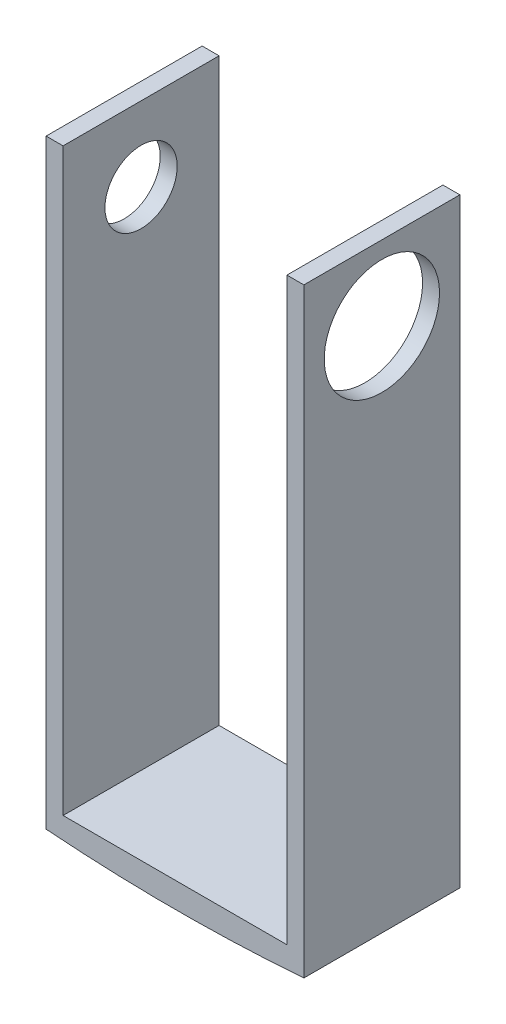
SolidWorks part; units mm, degrees
ref_plane "Front Plane" through (0, 0, 0) normal (0, 0, 1) x (1, 0, 0)
ref_plane "Top Plane" through (0, 0, 0) normal (0, 1, 0) x (1, 0, 0)
ref_plane "Right Plane" through (0, 0, 0) normal (1, 0, 0) x (0, 0, -1)
sketch "Sketch1" plane through (0, 0, 0) normal (0, 0, 1) x (1, 0, 0)
  line L0 (-3.3539, 20.1872) -> (-3.3539, -2.2918)
  line L1 (-3.3539, -2.2918) -> (6.2981, -2.2918)
  line L2 (6.2981, -2.2918) -> (6.2981, 20.1872)
  line L3 (5.6631, 20.1872) -> (5.6631, -1.5298)
  line L4 (5.6631, -1.5298) -> (-2.7189, -1.5298)
  line L5 (-2.7189, -1.5298) -> (-2.7189, 20.1872)
  line L6 (-2.7189, 20.1872) -> (-3.3539, 20.1872)
  line L7 (5.6631, 20.1872) -> (6.2981, 20.1872)
  dimension "D1" = 8.382
  dimension "D2" = 9.652
  dimension "D3" = 0.635
  dimension "D4" = 21.717
  dimension "D5" = 22.479
  dimension "D6" = 21.717
extrude "Boss-Extrude1" add sketch "Sketch1" along normal blind 5.842
sketch "Sketch2" plane through (-3.3539, 0, 0) normal (-1, 0, 0) x (0, 0, 1)
  line L0 (5.842, 20.1872) -> (0, 20.1872) construction
  line L1 (2.921, -2.2918) -> (2.921, 20.1872) construction
  point P0 (2.921, 17.3932)
  dimension "D1" = 2.794
hole_wizard "#6-32 Tapped Hole1" positions "Sketch3" profile "Sketch4" tap size "#6-32" standard "ANSI Inch" end condition up to next
sketch "Sketch3" plane through (-3.3539, 0, 0) normal (-1, 0, 0) x (0, 0, 1)
  point P0 (2.921, 17.3932)
sketch "Sketch4" plane through (-3.3539, 17.3932, 2.921) normal (0, 1, 0) x (0, 0, 1)
  line L0 (0, 0) -> (0, 0.635)
  line L1 (0, 0.635) -> (1.3525, 0.635)
  line L2 (1.3525, 0.635) -> (1.3525, 0)
  line L5 (1.3525, 0) -> (0, 0)
  line L11 (0, -6.35) -> (0, 107.95) construction
  dimension "Thread Major Dia." = 2.7051
  dimension "Thru Tap Drill Depth" = 0.635
sketch "Sketch5" plane through (6.2981, 0, 0) normal (1, 0, 0) x (0, 0, -1)
  point P0 (-2.921, 17.3932)
sketch "Sketch6" plane through (6.2981, 0, 0) normal (1, 0, 0) x (0, 0, -1)
  circle A0 centre (-2.921, 17.3932) radius 2.159
extrude "Cut-Extrude1" cut sketch "Sketch6" against normal up to next
sketch "Sketch12" plane through (-3.3539, 0, 0) normal (-1, 0, 0) x (0, 0, 1)
  line L0 (2.921, -2.2918) -> (2.921, 20.1872) construction
  line L1 (5.842, -2.2918) -> (0, -2.2918) construction
  line L2 (5.842, 20.1872) -> (0, 20.1872) construction
sketch "Sketch13" plane through (0, 0, 0) normal (0, 0, 1) x (1, 0, 0)
  line L0 (6.2981, -2.2918) -> (1.4721, 60.2603) construction
  line L1 (1.4721, 60.2603) -> (-3.3539, -2.2918) construction
  dimension "D1" = 62.738
  dimension "D2" = 62.738
sketch "Sketch15" plane through (0, 0, 0) normal (0, 0, 1) x (1, 0, 0)
  line L0 (-3.3539, -2.2918) -> (6.2981, -2.2918) construction
  line L1 (6.2981, -2.2918) -> (-3.3539, -2.2918)
  arc A0 (-3.3539, -2.2918) -> (6.2981, -2.2918) centre (1.4721, 60.2603) ccw
extrude "Boss-Extrude2" add sketch "Sketch15" along normal through all
sketch "Sketch18" plane through (-3.3539, 0, 0) normal (-1, 0, 0) x (0, 0, 1)
  line L0 (2.921, -2.2918) -> (2.921, 20.1872) construction
  point P0 (2.921, 11.1176)
  point P1 (2.921, 8.9477)
sketch "Sketch25" plane through (-3.3539, 0, 0) normal (-1, 0, 0) x (0, 0, 1)
  line L0 (2.921, -2.2918) -> (2.921, 20.1872) construction
  point P0 (2.921, 13.3767)
